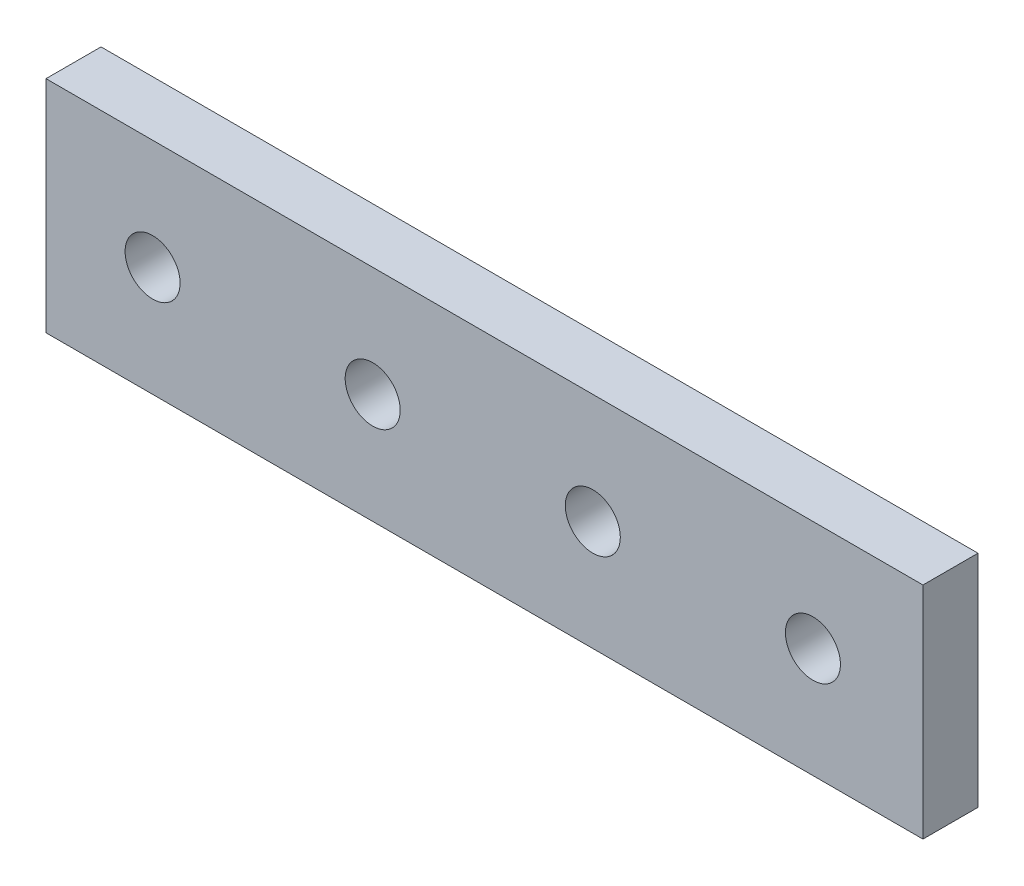
SolidWorks part; units mm, degrees
ref_plane "Front Plane" through (0, 0, 0) normal (0, 0, 1) x (1, 0, 0)
ref_plane "Top Plane" through (0, 0, 0) normal (0, 1, 0) x (1, 0, 0)
ref_plane "Right Plane" through (0, 0, 0) normal (1, 0, 0) x (0, 0, -1)
sketch "Sketch1" plane through (0, 0, 0) normal (0, 0, 1) x (1, 0, 0)
  line L1 (-50.6, -12.7) -> (50.6, -12.7)
  line L2 (-50.6, -12.7) -> (-50.6, 12.7)
  line L3 (-50.6, 12.7) -> (50.6, 12.7)
  line L4 (50.6, -12.7) -> (50.6, 12.7)
  line L5 (-50.6, -12.7) -> (50.6, 12.7) construction
  line L6 (-50.6, 12.7) -> (50.6, -12.7) construction
  point P0 (0, 0)
  dimension "D1" = 101.2
  dimension "D2" = 25.4
extrude "Boss-Extrude1" add sketch "Sketch1" along normal blind 6.35
sketch "Sketch2" plane through (0, 0, 6.35) normal (0, 0, 1) x (1, 0, 0)
  line L0 (0, 0) -> (-50.6, 0) construction
  line L1 (-50.6, 12.7) -> (-50.6, -12.7) construction
  line L2 (0, 0) -> (50.6, 0) construction
  line L3 (50.6, -12.7) -> (50.6, 12.7) construction
  circle A0 centre (-38.3, 0) radius 3.175
  circle A2 centre (12.5, 0) radius 3.175
  circle A3 centre (37.9, 0) radius 3.175
  circle A4 centre (-12.9, 0) radius 3.175
  dimension "D1" = 6.35
  dimension "D2" = 6.35
  dimension "D3" = 6.35
  dimension "D4" = 25.4
  dimension "D5" = 25.4
  dimension "D6" = 12.7
  dimension "D7" = 6.35
  dimension "D8" = 25.4
extrude "Cut-Extrude1" cut sketch "Sketch2" against normal blind 6.35
